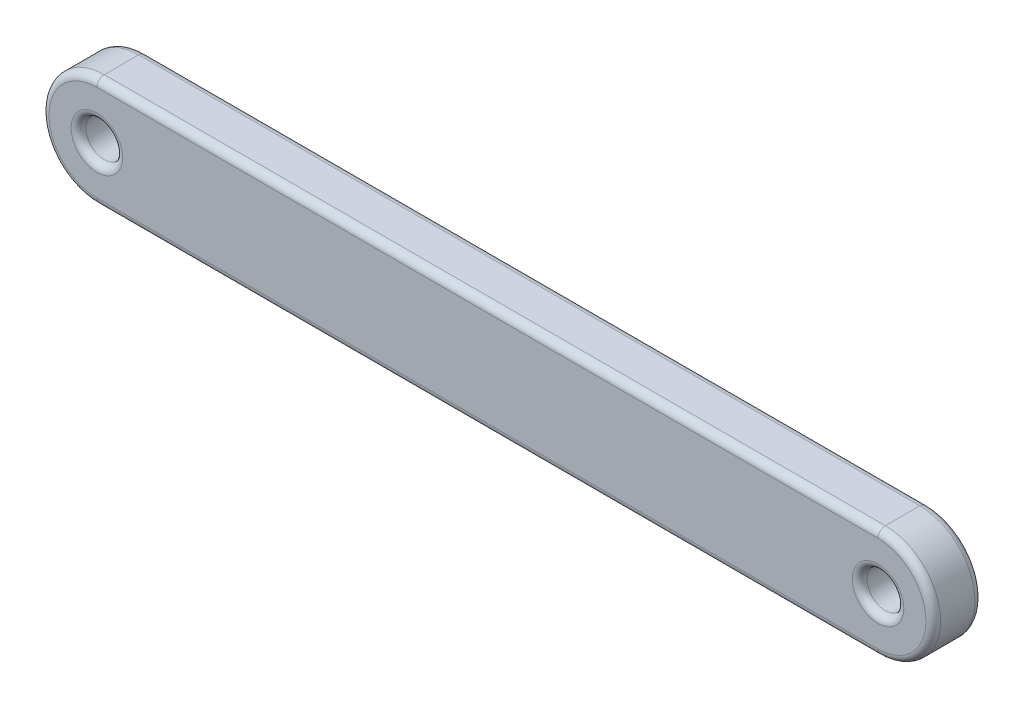
SolidWorks part; units mm, degrees
ref_plane "Front" through (0, 0, 0) normal (0, 0, 1) x (1, 0, 0)
ref_plane "Top" through (0, 0, 0) normal (0, 1, 0) x (1, 0, 0)
ref_plane "Right" through (0, 0, 0) normal (1, 0, 0) x (0, 0, -1)
sketch "Sketch1" plane through (0, 0, 0) normal (0, 0, 1) x (1, 0, 0)
  line L0 (0, 0) -> (31.8283, 0) construction
  line L1 (0, 2.25) -> (31.8283, 2.25)
  line L2 (0, -2.25) -> (31.8283, -2.25)
  circle A0 centre (0, 0) radius 0.75
  arc A1 (0, 2.25) -> (0, -2.25) centre (0, 0) ccw
  arc A2 (31.8283, -2.25) -> (31.8283, 2.25) centre (31.8283, 0) ccw
  circle A3 centre (31.8283, 0) radius 0.75
  point P3 (15.9141, 0)
  dimension "D1" = 1.5
  dimension "D2" = 31.8283
  dimension "D3" = 1.5
extrude "Boss-Extrude1" add sketch "Sketch1" along normal blind 2
fillet "Fillet1" radius 0.3 12 edges at (32.5783, 0, 0) (0.75, 0, 0) (34.0783, 0, 0) (-2.25, 0, 0) (32.5783, 0, 2) (0.75, 0, 2) (34.0783, 0, 2) (-2.25, 0, 2) (15.9141, -2.25, 0) (15.9141, -2.25, 2) (15.9141, 2.25, 0) (15.9141, 2.25, 2)
